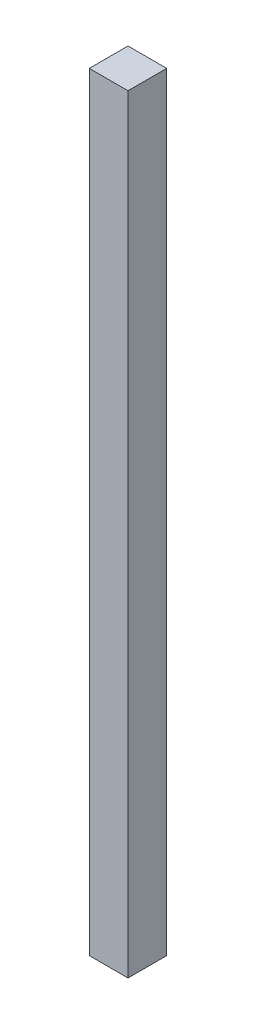
SolidWorks part; units mm, degrees
ref_plane "Front Plane" through (0, 0, 0) normal (0, 0, 1) x (1, 0, 0)
ref_plane "Top Plane" through (0, 0, 0) normal (0, 1, 0) x (1, 0, 0)
ref_plane "Right Plane" through (0, 0, 0) normal (1, 0, 0) x (0, 0, -1)
sketch "Sketch1" plane through (0, 0, 0) normal (0, 1, 0) x (1, 0, 0)
  line L1 (0, 0) -> (25.4, 0)
  line L2 (0, 0) -> (0, 25.4)
  line L3 (0, 25.4) -> (25.4, 25.4)
  line L4 (25.4, 0) -> (25.4, 25.4)
  dimension "D1" = 25.4
  dimension "D2" = 25.4
extrude "Boss-Extrude1" add sketch "Sketch1" along normal blind 503.682
